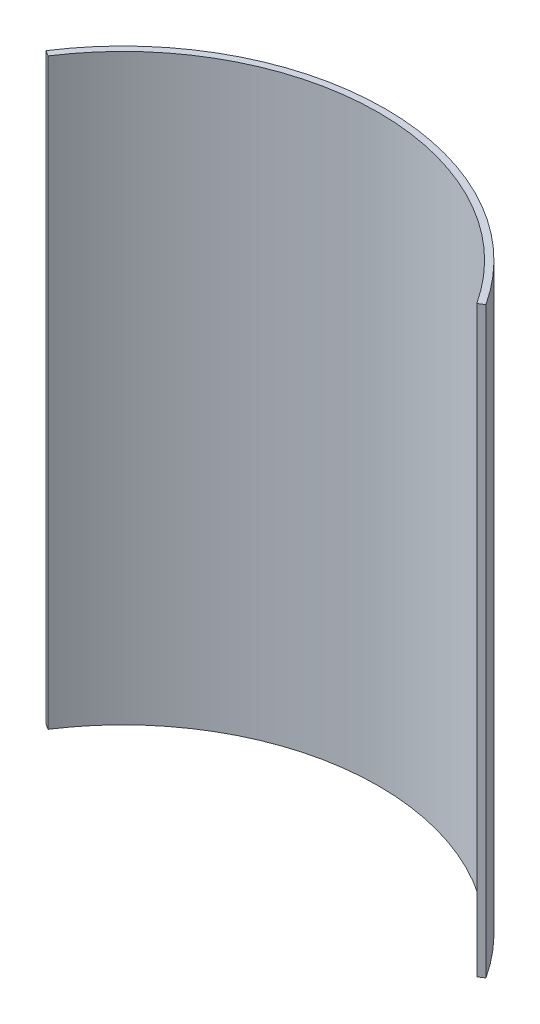
SolidWorks part; units mm, degrees
ref_plane "Front Plane" through (0, 0, 0) normal (0, 0, 1) x (1, 0, 0)
ref_plane "Top Plane" through (0, 0, 0) normal (0, 1, 0) x (1, 0, 0)
ref_plane "Right Plane" through (0, 0, 0) normal (1, 0, 0) x (0, 0, -1)
sketch "Sketch1" plane through (0, 0, 0) normal (0, 1, 0) x (1, 0, 0)
  line L0 (0, 45.7344) -> (0, 0) construction
  line L1 (32.1018, 19.4227) -> (31.43, 20.4549) construction
  line L3 (-31.43, 20.4549) -> (-32.2437, 20.9844)
  line L4 (39.6072, -22.8672) -> (0, 0) construction
  line L7 (-39.6072, -22.8672) -> (0, 0) construction
  line L8 (31.43, 20.4549) -> (32.2437, 20.9844)
  arc A2 (32.2437, 20.9844) -> (-32.2437, 20.9844) centre (0, 0) ccw
  arc A3 (31.43, 20.4549) -> (-31.43, 20.4549) centre (0, 0) ccw
  arc A4 (31.4297, 19.878) -> (-31.4297, 19.878) centre (0, -0.5774) ccw construction
  dimension "D1" = 74.539
  dimension "D4" = 3
extrude "Boss-Extrude1" add sketch "Sketch1" against normal blind 85.5
